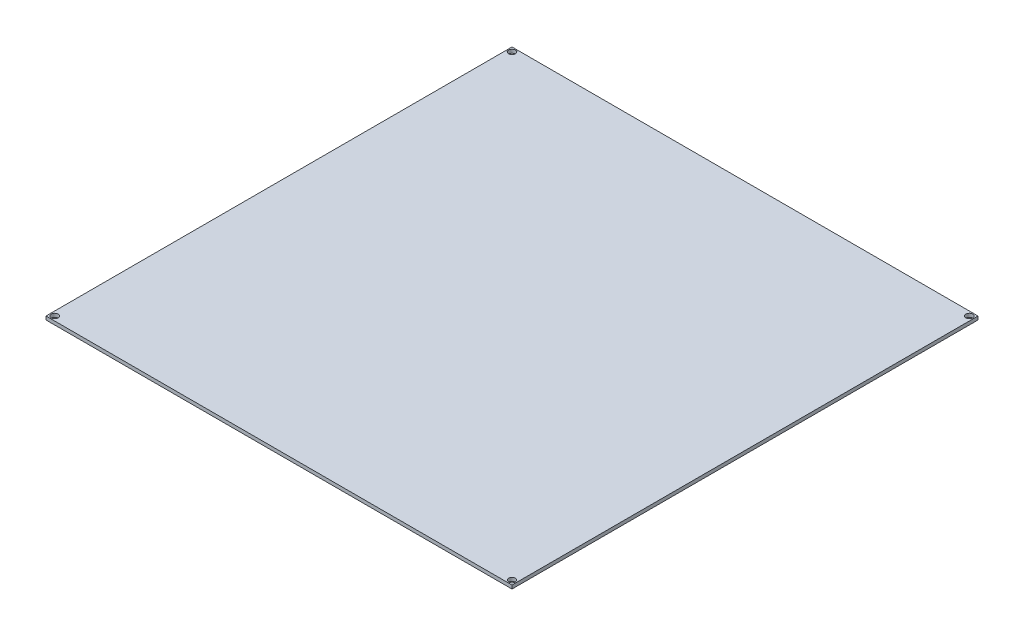
SolidWorks part; units mm, degrees
ref_plane "Front Plane" through (0, 0, 0) normal (0, 0, 1) x (1, 0, 0)
ref_plane "Top Plane" through (0, 0, 0) normal (0, 1, 0) x (1, 0, 0)
ref_plane "Right Plane" through (0, 0, 0) normal (1, 0, 0) x (0, 0, -1)
sketch "Sketch1" plane through (0, 0, 0) normal (0, 1, 0) x (1, 0, 0)
  line L1 (107, 107) -> (-107, 107)
  line L2 (107, 107) -> (107, -107)
  line L3 (107, -107) -> (-107, -107)
  line L4 (-107, 107) -> (-107, -107)
  line L5 (0, -107) -> (0, 107) construction
  line L6 (107, 0) -> (-107, 0) construction
  point P0 (0, 0)
  dimension "D1" = 214
  dimension "D2" = 214
extrude "Boss-Extrude1" add sketch "Sketch1" along normal blind 1.6 contours L2 L3 L4 L1
hole_wizard "M2.5 Clearance Hole1" positions "Sketch4" profile "Sketch3" hole size "M2.5" standard "ANSI Metric"
sketch "Sketch4" plane through (0, 1.6, 0) normal (0, 1, 0) x (1, 0, 0)
  line L0 (-105, 105) -> (105, 105) construction
  line L1 (-105, 105) -> (-105, -105) construction
  line L2 (-107, 107) -> (-107, -107) construction
  line L3 (107, 107) -> (-107, 107) construction
  point P0 (-105, 105)
  point P7 (105, 105)
  point P8 (105, -105)
  point P9 (-105, -105)
  dimension "D3" = 90
  dimension "D4" = 210
  dimension "D5" = 210
  dimension "D6" = 2
  dimension "D7" = 2
  dimension "D1" = 2
  dimension "D2" = 2
sketch "Sketch3" plane through (-105, 1.6, -105) normal (1, 0, 0) x (0, 0, 1)
  line L0 (0, 0) -> (0, 12.8693)
  line L1 (0, 12.8693) -> (1.55, 11.938)
  line L2 (1.55, 11.938) -> (1.55, 0)
  line L5 (1.55, 0) -> (0, 0)
  line L10 (0, 12.8693) -> (-1.55, 11.938) construction
  line L11 (0, -6.35) -> (0, 107.95) construction
  dimension "Hole Dia." = 3.1
  dimension "Hole Depth" = 11.938
  dimension "Drill Angle" = 118
